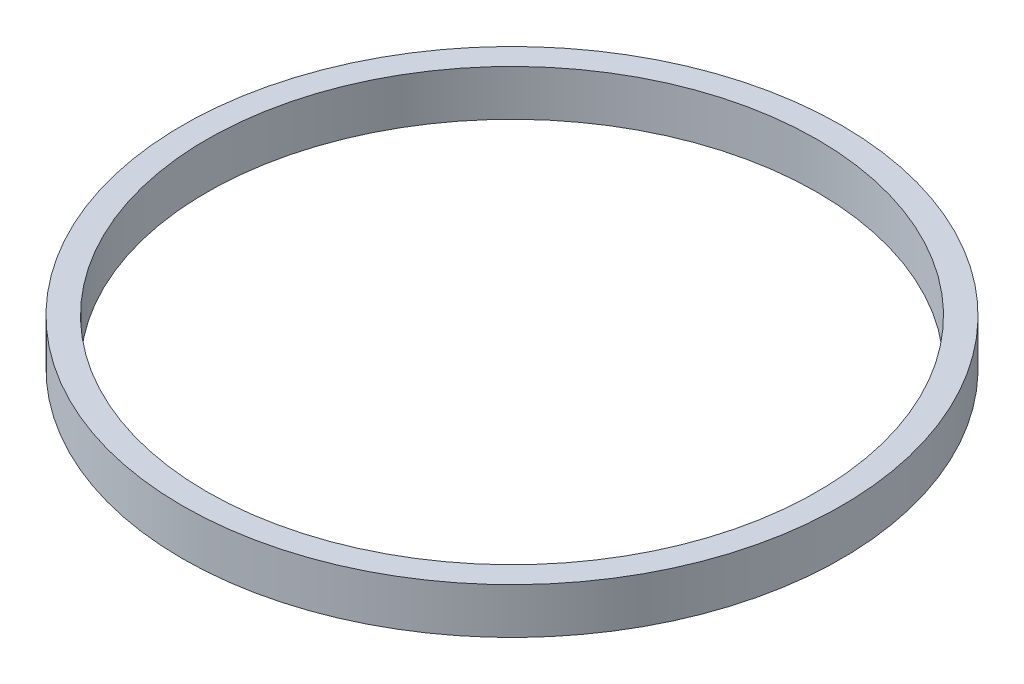
SolidWorks part; units mm, degrees
ref_plane "前视基准面" through (0, 0, 0) normal (0, 0, 1) x (1, 0, 0)
ref_plane "上视基准面" through (0, 0, 0) normal (0, 1, 0) x (1, 0, 0)
ref_plane "右视基准面" through (0, 0, 0) normal (1, 0, 0) x (0, 0, -1)
sketch "草图1" plane through (0, 0, 0) normal (0, 1, 0) x (1, 0, 0)
  circle A0 centre (-71.7106, 45.3554) radius 100
  circle A3 centre (-71.7106, 45.3554) radius 108
extrude "凸台-拉伸1" add sketch "草图1" along normal blind 15
